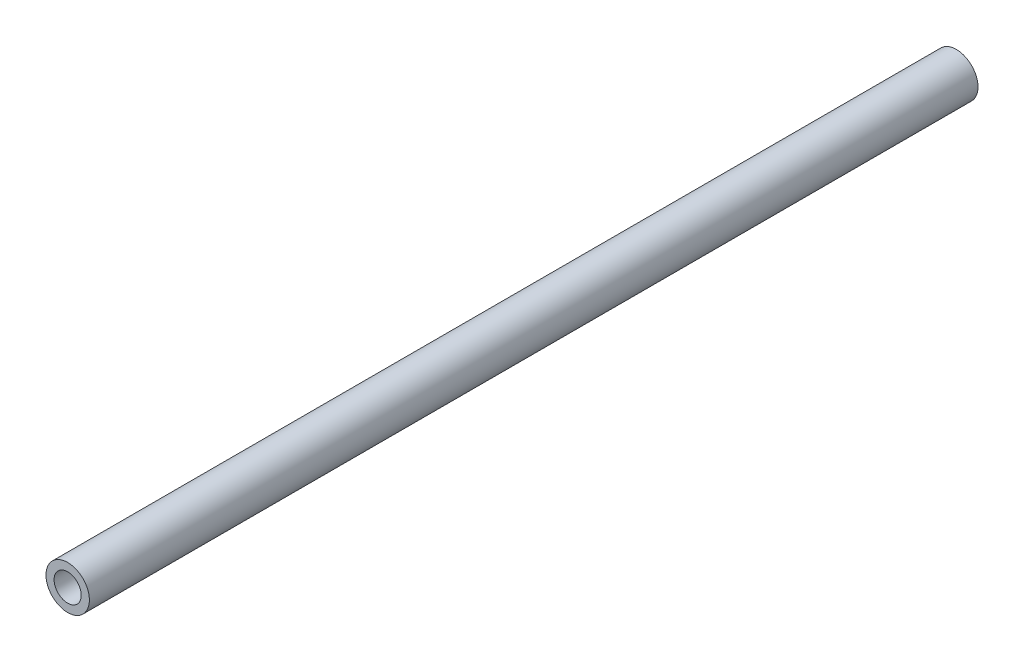
SolidWorks part; units mm, degrees
material "AISI 304"
ref_plane "Front Plane" through (0, 0, 0) normal (0, 0, 1) x (1, 0, 0)
ref_plane "Top Plane" through (0, 0, 0) normal (0, 1, 0) x (1, 0, 0)
ref_plane "Right Plane" through (0, 0, 0) normal (1, 0, 0) x (0, 0, -1)
sketch "Sketch1" plane through (0, 0, 0) normal (0, 0, 1) x (1, 0, 0)
  circle A0 centre (0, 0) radius 8.55
  circle A1 centre (0, 0) radius 5.35
  dimension "D1" = 10.7
  dimension "D2" = 17.1
extrude "Boss-Extrude1" add sketch "Sketch1" against normal blind 350
